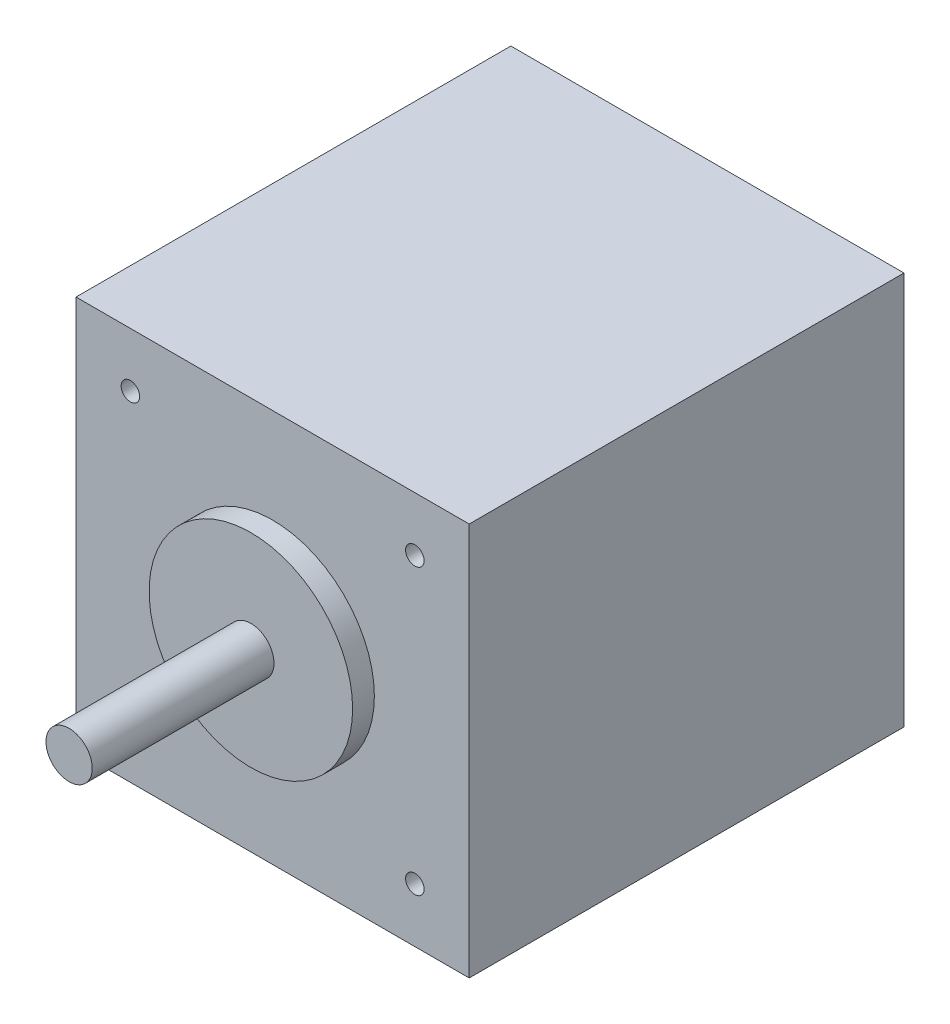
SolidWorks part; units mm, degrees
ref_plane "Front Plane" through (0, 0, 0) normal (0, 0, 1) x (1, 0, 0)
ref_plane "Top Plane" through (0, 0, 0) normal (0, 1, 0) x (1, 0, 0)
ref_plane "Right Plane" through (0, 0, 0) normal (1, 0, 0) x (0, 0, -1)
sketch "Sketch1" plane through (0, 0, 0) normal (0, 0, 1) x (1, 0, 0)
  line L1 (-21.25, 21.25) -> (21.25, 21.25)
  line L2 (-21.25, 21.25) -> (-21.25, -21.25)
  line L3 (-21.25, -21.25) -> (21.25, -21.25)
  line L4 (21.25, 21.25) -> (21.25, -21.25)
  line L5 (-21.25, 21.25) -> (21.25, -21.25) construction
  line L6 (-21.25, -21.25) -> (21.25, 21.25) construction
  point P0 (0, 0)
  dimension "D1" = 42.5
extrude "Boss-Extrude1" add sketch "Sketch1" along normal blind 47
sketch "Sketch2" plane through (0, 0, 47) normal (0, 0, 1) x (1, 0, 0)
  line L1 (-15.375, 15.375) -> (15.375, 15.375) construction
  line L2 (-15.375, 15.375) -> (-15.375, -15.375) construction
  line L3 (-15.375, -15.375) -> (15.375, -15.375) construction
  line L4 (15.375, 15.375) -> (15.375, -15.375) construction
  line L5 (-15.375, 15.375) -> (15.375, -15.375) construction
  line L6 (-15.375, -15.375) -> (15.375, 15.375) construction
  circle A0 centre (-15.375, 15.375) radius 1
  circle A1 centre (15.375, 15.375) radius 1
  circle A2 centre (15.375, -15.375) radius 1
  circle A3 centre (-15.375, -15.375) radius 1
  point P0 (0, 0)
  dimension "D1" = 2
  dimension "D2" = 30.75
extrude "Cut-Extrude1" cut sketch "Sketch2" against normal blind 2
sketch "Sketch3" plane through (0, 0, 47) normal (0, 0, 1) x (1, 0, 0)
  circle A0 centre (0, 0) radius 2.5
  dimension "D1" = 5
extrude "Boss-Extrude2" add sketch "Sketch3" along normal blind 22
sketch "Sketch4" plane through (0, 0, 47) normal (0, 0, 1) x (1, 0, 0)
  circle A0 centre (0, 0) radius 11
  dimension "D1" = 22
extrude "Boss-Extrude3" add sketch "Sketch4" along normal blind 2.35
